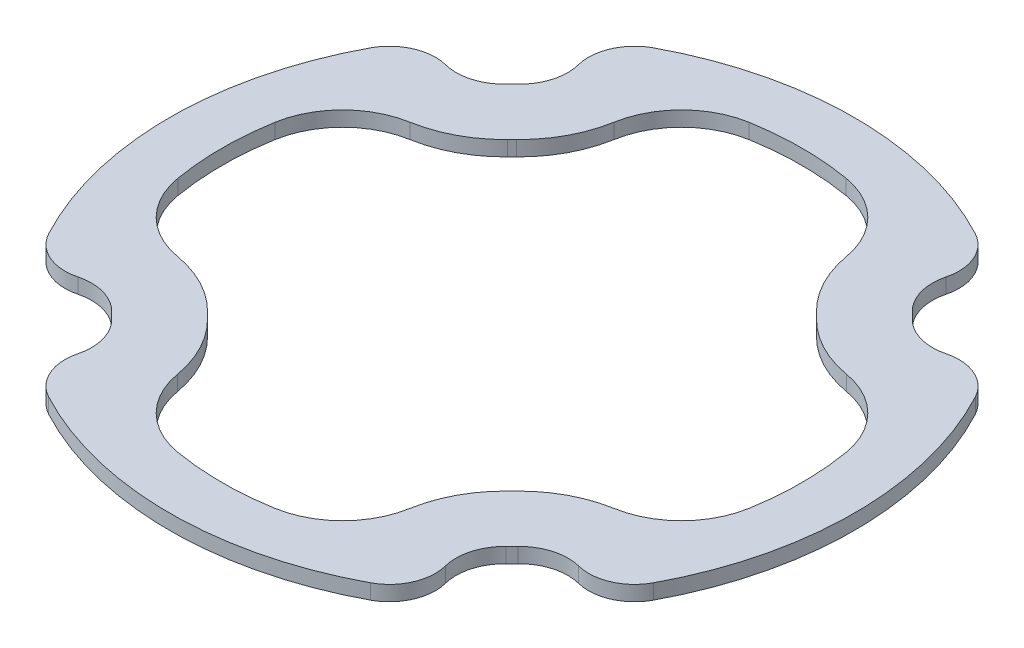
SolidWorks part; units mm, degrees
material "ABS PC"
ref_plane "Front Plane" through (0, 0, 0) normal (0, 0, 1) x (1, 0, 0)
ref_plane "Top Plane" through (0, 0, 0) normal (0, 1, 0) x (1, 0, 0)
ref_plane "Right Plane" through (0, 0, 0) normal (1, 0, 0) x (0, 0, -1)
sketch "Flange Ref" plane through (0, 0, 0) normal (0, 1, 0) x (1, 0, 0)
  arc A0 (0, 23) -> (-10.8015, 20.3058) centre (0, 0) ccw construction
  arc A1 (-10.8015, 20.3058) -> (-12.4493, 16.5701) centre (-9.2508, 17.3906) ccw construction
  arc A2 (-13.266, 13.6717) -> (-12.4493, 16.5701) centre (-15.3552, 15.8247) ccw construction
  arc A3 (-13.266, 13.6717) -> (-13.6717, 13.266) centre (0, 0) ccw construction
  arc A4 (-16.5701, 12.4493) -> (-13.6717, 13.266) centre (-15.8247, 15.3552) ccw construction
  arc A5 (-16.5701, 12.4493) -> (-17.3906, 12.5528) centre (-17.3906, 9.2508) ccw construction
  arc A6 (-17.3906, 12.5528) -> (-20.3058, 10.8015) centre (-17.3906, 9.2508) ccw construction
  arc A7 (-20.3058, 10.8015) -> (-20.3058, -10.8015) centre (0, 0) ccw construction
  circle A8 centre (0, 0) radius 25 construction
  arc A9 (10.8015, 20.3058) -> (-10.8015, 20.3058) centre (0, 0) ccw construction
  arc A10 (12.5528, 17.3906) -> (10.8015, 20.3058) centre (9.2508, 17.3906) ccw construction
  arc A11 (12.4493, 16.5701) -> (12.5528, 17.3906) centre (9.2508, 17.3906) ccw construction
  arc A12 (12.4493, 16.5701) -> (13.266, 13.6717) centre (15.3552, 15.8247) ccw construction
  arc A13 (13.6717, 13.266) -> (13.266, 13.6717) centre (0, 0) ccw construction
  arc A14 (13.6717, 13.266) -> (16.5701, 12.4493) centre (15.8247, 15.3552) ccw construction
  arc A15 (20.3058, 10.8015) -> (16.5701, 12.4493) centre (17.3906, 9.2508) ccw construction
  arc A16 (23, 0) -> (20.3058, 10.8015) centre (0, 0) ccw construction
  arc A17 (20.3058, -10.8015) -> (20.3058, 10.8015) centre (0, 0) ccw construction
  arc A18 (17.3906, -12.5528) -> (20.3058, -10.8015) centre (17.3906, -9.2508) ccw construction
  arc A19 (16.5701, -12.4493) -> (17.3906, -12.5528) centre (17.3906, -9.2508) ccw construction
  arc A20 (16.5701, -12.4493) -> (13.6717, -13.266) centre (15.8247, -15.3552) ccw construction
  arc A21 (13.266, -13.6717) -> (13.6717, -13.266) centre (0, 0) ccw construction
  arc A22 (13.266, -13.6717) -> (12.4493, -16.5701) centre (15.3552, -15.8247) ccw construction
  arc A23 (10.8015, -20.3058) -> (12.4493, -16.5701) centre (9.2508, -17.3906) ccw construction
  arc A24 (0, -23) -> (10.8015, -20.3058) centre (0, 0) ccw construction
  arc A25 (-10.8015, -20.3058) -> (10.8015, -20.3058) centre (0, 0) ccw construction
  arc A26 (-12.5528, -17.3906) -> (-10.8015, -20.3058) centre (-9.2508, -17.3906) ccw construction
  arc A27 (-12.4493, -16.5701) -> (-12.5528, -17.3906) centre (-9.2508, -17.3906) ccw construction
  arc A28 (-12.4493, -16.5701) -> (-13.266, -13.6717) centre (-15.3552, -15.8247) ccw construction
  arc A29 (-13.6717, -13.266) -> (-13.266, -13.6717) centre (0, 0) ccw construction
  arc A30 (-13.6717, -13.266) -> (-16.5701, -12.4493) centre (-15.8247, -15.3552) ccw construction
  arc A31 (-20.3058, -10.8015) -> (-16.5701, -12.4493) centre (-17.3906, -9.2508) ccw construction
  arc A32 (-23, 0) -> (-20.3058, -10.8015) centre (0, 0) ccw construction
  arc A33 (-4.75, -14.1421) -> (4.75, -14.1421) centre (0, -14.1421) ccw construction
  arc A34 (4.75, -14.1421) -> (-4.75, -14.1421) centre (0, -14.1421) ccw construction
  arc A35 (9.3921, 0) -> (18.8921, 0) centre (14.1421, 0) ccw construction
  arc A36 (18.8921, 0) -> (9.3921, 0) centre (14.1421, 0) ccw construction
  arc A37 (-4.75, 14.1421) -> (4.75, 14.1421) centre (0, 14.1421) ccw construction
  arc A38 (4.75, 14.1421) -> (-4.75, 14.1421) centre (0, 14.1421) ccw construction
  arc A39 (-18.8921, 0) -> (-9.3921, 0) centre (-14.1421, 0) ccw construction
  arc A40 (-9.3921, 0) -> (-18.8921, 0) centre (-14.1421, 0) ccw construction
  point P63 (0, 0)
  dimension "D1" = 50
sketch "Internal Slab" plane through (0, 0, 0) normal (0, 1, 0) x (1, 0, 0)
  arc A0 (20.0851, 10.6841) -> (16.6323, 12.2071) centre (17.3906, 9.2508) ccw
  arc A1 (13.4923, 13.0919) -> (16.6323, 12.2071) centre (15.8247, 15.3552) ccw
  arc A2 (12.2071, 16.6323) -> (13.0919, 13.4923) centre (15.3552, 15.8247) ccw
  arc A3 (12.3028, 17.3906) -> (10.6841, 20.0851) centre (9.2508, 17.3906) ccw
  arc A4 (12.2071, 16.6323) -> (12.3028, 17.3906) centre (9.2508, 17.3906) ccw
  arc A5 (13.4923, 13.0919) -> (13.0919, 13.4923) centre (0, 0) ccw
  arc A6 (10.6841, -20.0851) -> (12.2071, -16.6323) centre (9.2508, -17.3906) ccw
  arc A7 (13.0919, -13.4923) -> (12.2071, -16.6323) centre (15.3552, -15.8247) ccw
  arc A8 (16.6323, -12.2071) -> (13.4923, -13.0919) centre (15.8247, -15.3552) ccw
  arc A9 (17.3906, -12.3028) -> (20.0851, -10.6841) centre (17.3906, -9.2508) ccw
  arc A10 (16.6323, -12.2071) -> (17.3906, -12.3028) centre (17.3906, -9.2508) ccw
  arc A11 (13.0919, -13.4923) -> (13.4923, -13.0919) centre (0, 0) ccw
  arc A12 (-20.0851, -10.6841) -> (-16.6323, -12.2071) centre (-17.3906, -9.2508) ccw
  arc A13 (-13.4923, -13.0919) -> (-16.6323, -12.2071) centre (-15.8247, -15.3552) ccw
  arc A14 (-12.2071, -16.6323) -> (-13.0919, -13.4923) centre (-15.3552, -15.8247) ccw
  arc A15 (-12.3028, -17.3906) -> (-10.6841, -20.0851) centre (-9.2508, -17.3906) ccw
  arc A16 (-12.2071, -16.6323) -> (-12.3028, -17.3906) centre (-9.2508, -17.3906) ccw
  arc A17 (-13.4923, -13.0919) -> (-13.0919, -13.4923) centre (0, 0) ccw
  arc A18 (-20.0851, 10.6841) -> (-20.0851, -10.6841) centre (0, 0) ccw
  arc A19 (10.6841, 20.0851) -> (-10.6841, 20.0851) centre (0, 0) ccw
  arc A20 (20.0851, -10.6841) -> (20.0851, 10.6841) centre (0, 0) ccw
  arc A21 (-10.6841, -20.0851) -> (10.6841, -20.0851) centre (0, 0) ccw
  arc A122 (-10.6841, 20.0851) -> (-12.2071, 16.6323) centre (-9.2508, 17.3906) ccw
  arc A123 (-13.0919, 13.4923) -> (-13.4923, 13.0919) centre (0, 0) ccw
  arc A124 (-13.0919, 13.4923) -> (-12.2071, 16.6323) centre (-15.3552, 15.8247) ccw
  arc A125 (-16.6323, 12.2071) -> (-17.3906, 12.3028) centre (-17.3906, 9.2508) ccw
  arc A126 (-16.6323, 12.2071) -> (-13.4923, 13.0919) centre (-15.8247, 15.3552) ccw
  arc A127 (-17.3906, 12.3028) -> (-20.0851, 10.6841) centre (-17.3906, 9.2508) ccw
  arc A128 (-10.6841, 20.0851) -> (-12.2071, 16.6323) centre (-9.2508, 17.3906) ccw
  arc A129 (-13.0919, 13.4923) -> (-13.4923, 13.0919) centre (0, 0) ccw
  arc A130 (-13.0919, 13.4923) -> (-12.2071, 16.6323) centre (-15.3552, 15.8247) ccw
  arc A131 (-16.6323, 12.2071) -> (-17.3906, 12.3028) centre (-17.3906, 9.2508) ccw
  arc A132 (-16.6323, 12.2071) -> (-13.4923, 13.0919) centre (-15.8247, 15.3552) ccw
  arc A133 (-17.3906, 12.3028) -> (-20.0851, 10.6841) centre (-17.3906, 9.2508) ccw
  point P1 (0, 0)
  point P40 (0, 0)
  dimension "D1" = 0.25
  dimension "D2" = 4
extrude "PCB Outline Outer" add sketch "Internal Slab" along normal blind 1
sketch "PCB Outline Inner" plane through (0, 0, 0) normal (0, 1, 0) x (1, 0, 0)
  line L0 (0, 0) -> (-31.5542, 0) construction
  line L1 (-31.5542, 0) -> (-33.9533, 6.1655) construction
  line L2 (-33.9533, 6.1655) -> (-33.8659, 6.1654) construction
  line L3 (0, 0) -> (0, 27.5562) construction
  arc A63 (-14.5834, 8.2122) -> (-19.4715, 3.3048) centre (-13.5561, 2.3008) ccw
  arc A65 (-8.2122, 14.5834) -> (-3.3048, 19.4715) centre (-2.3008, 13.5561) cw
  arc A66 (-10.3064, 10.6216) -> (-10.6216, 10.3064) centre (0, 0) ccw
  arc A67 (-10.3064, 10.6216) -> (-8.3325, 17.6262) centre (-15.3552, 15.8247) ccw
  arc A68 (-17.6262, 8.3325) -> (-10.6216, 10.3064) centre (-15.8247, 15.3552) ccw
  arc A69 (-10.3064, 10.6216) -> (-10.6216, 10.3064) centre (0, 0) ccw
  arc A70 (-10.3064, 10.6216) -> (-8.2122, 14.5834) centre (-15.3552, 15.8247) ccw
  arc A71 (-14.5834, 8.2122) -> (-10.6216, 10.3064) centre (-15.8247, 15.3552) ccw
  arc A72 (9.2752, 17.4365) -> (-9.2752, 17.4365) centre (0, 0) ccw
  arc A73 (0, 19.75) -> (-3.3048, 19.4715) centre (0, 0) ccw
  arc A74 (3.3048, 19.4715) -> (0, 19.75) centre (0, 0) ccw
  arc A75 (8.2122, 14.5834) -> (3.3048, 19.4715) centre (2.3008, 13.5561) ccw
  arc A76 (8.2122, 14.5834) -> (10.3064, 10.6216) centre (15.3552, 15.8247) ccw
  arc A77 (10.6216, 10.3064) -> (10.3064, 10.6216) centre (0, 0) ccw
  arc A78 (10.6216, 10.3064) -> (14.5834, 8.2122) centre (15.8247, 15.3552) ccw
  arc A79 (14.5834, 8.2122) -> (19.4715, 3.3048) centre (13.5561, 2.3008) cw
  arc A80 (19.75, 0) -> (19.4715, 3.3048) centre (0, 0) ccw
  arc A81 (19.4715, -3.3048) -> (19.75, 0) centre (0, 0) ccw
  arc A82 (14.5834, -8.2122) -> (19.4715, -3.3048) centre (13.5561, -2.3008) ccw
  arc A83 (14.5834, -8.2122) -> (10.6216, -10.3064) centre (15.8247, -15.3552) ccw
  arc A84 (10.3064, -10.6216) -> (10.6216, -10.3064) centre (0, 0) ccw
  arc A85 (10.3064, -10.6216) -> (8.2122, -14.5834) centre (15.3552, -15.8247) ccw
  arc A86 (8.2122, -14.5834) -> (3.3048, -19.4715) centre (2.3008, -13.5561) cw
  arc A87 (0, -19.75) -> (3.3048, -19.4715) centre (0, 0) ccw
  arc A88 (-3.3048, -19.4715) -> (0, -19.75) centre (0, 0) ccw
  arc A89 (-8.2122, -14.5834) -> (-3.3048, -19.4715) centre (-2.3008, -13.5561) ccw
  arc A90 (-8.2122, -14.5834) -> (-10.3064, -10.6216) centre (-15.3552, -15.8247) ccw
  arc A91 (-10.6216, -10.3064) -> (-10.3064, -10.6216) centre (0, 0) ccw
  arc A92 (-10.6216, -10.3064) -> (-14.5834, -8.2122) centre (-15.8247, -15.3552) ccw
  arc A93 (-14.5834, -8.2122) -> (-19.4715, -3.3048) centre (-13.5561, -2.3008) cw
  arc A94 (-19.75, 0) -> (-19.4715, -3.3048) centre (0, 0) ccw
  arc A146 (-17.4365, 9.2752) -> (-17.4365, -9.2752) centre (0, 0) ccw
  arc A147 (-19.4715, 3.3048) -> (-19.75, 0) centre (0, 0) ccw
  point P57 (0, 0)
  dimension "D3" = 6
  dimension "D5" = 6
  dimension "D1" = 3
  dimension "D2" = 4
  dimension "D4" = 3
  dimension "D6" = 4
sketch "LED Alignment Reference" [suppressed] plane through (0, 1.6, 0) normal (0, 1, 0) x (1, 0, 0)
  line L0 (0, 0) -> (0, 23.3583)
  line L1 (0, 0) -> (6.0456, 22.5624)
  line L2 (0, 0) -> (11.6791, 20.2289)
  line L3 (0, 0) -> (16.5168, 16.5168)
  line L4 (0, 0) -> (20.2289, 11.6791)
  line L5 (0, 0) -> (22.5624, 6.0456)
  line L6 (0, 0) -> (23.3583, 0)
  line L7 (0, 0) -> (22.5624, -6.0456)
  line L8 (0, 0) -> (20.2289, -11.6791)
  line L9 (0, 0) -> (16.5168, -16.5168)
  line L10 (0, 0) -> (11.6791, -20.2289)
  line L11 (0, 0) -> (6.0456, -22.5624)
  line L12 (0, 0) -> (0, -23.3583)
  line L13 (0, 0) -> (-6.0456, -22.5624)
  line L14 (0, 0) -> (-11.6791, -20.2289)
  line L15 (0, 0) -> (-16.5168, -16.5168)
  line L16 (0, 0) -> (-20.2289, -11.6791)
  line L17 (0, 0) -> (-22.5624, -6.0456)
  line L18 (0, 0) -> (-23.3583, 0)
  line L19 (0, 0) -> (-22.5624, 6.0456)
  line L20 (0, 0) -> (-20.2289, 11.6791)
  line L21 (0, 0) -> (-16.5168, 16.5168)
  line L22 (0, 0) -> (-11.6791, 20.2289)
  line L23 (0, 0) -> (-6.0456, 22.5624)
  arc A93 (18.5401, -9.8623) -> (18.5401, 9.8623) centre (0, 0) ccw
  arc A94 (18.5401, 9.8623) -> (17.0671, 10.512) centre (17.3906, 9.2508) ccw
  arc A95 (12.2363, 11.8733) -> (17.0671, 10.512) centre (15.8247, 15.3552) ccw
  arc A96 (12.2363, 11.8733) -> (11.8733, 12.2363) centre (0, 0) ccw
  arc A97 (10.512, 17.0671) -> (11.8733, 12.2363) centre (15.3552, 15.8247) ccw
  arc A98 (10.512, 17.0671) -> (9.8623, 18.5401) centre (9.2508, 17.3906) ccw
  arc A99 (9.8623, 18.5401) -> (-9.8623, 18.5401) centre (0, 0) ccw
  arc A100 (-9.8623, 18.5401) -> (-10.512, 17.0671) centre (-9.2508, 17.3906) ccw
  arc A101 (-11.8733, 12.2363) -> (-10.512, 17.0671) centre (-15.3552, 15.8247) ccw
  arc A102 (-11.8733, 12.2363) -> (-12.2363, 11.8733) centre (0, 0) ccw
  arc A103 (-17.0671, 10.512) -> (-12.2363, 11.8733) centre (-15.8247, 15.3552) ccw
  arc A104 (-17.0671, 10.512) -> (-18.5401, 9.8623) centre (-17.3906, 9.2508) ccw
  arc A105 (-18.5401, 9.8623) -> (-18.5401, -9.8623) centre (0, 0) ccw
  arc A106 (-18.5401, -9.8623) -> (-17.0671, -10.512) centre (-17.3906, -9.2508) ccw
  arc A107 (-12.2363, -11.8733) -> (-17.0671, -10.512) centre (-15.8247, -15.3552) ccw
  arc A108 (-12.2363, -11.8733) -> (-11.8733, -12.2363) centre (0, 0) ccw
  arc A109 (-10.512, -17.0671) -> (-11.8733, -12.2363) centre (-15.3552, -15.8247) ccw
  arc A110 (-10.512, -17.0671) -> (-9.8623, -18.5401) centre (-9.2508, -17.3906) ccw
  arc A111 (-9.8623, -18.5401) -> (9.8623, -18.5401) centre (0, 0) ccw
  arc A112 (9.8623, -18.5401) -> (10.512, -17.0671) centre (9.2508, -17.3906) ccw
  arc A113 (11.8733, -12.2363) -> (10.512, -17.0671) centre (15.3552, -15.8247) ccw
  arc A114 (11.8733, -12.2363) -> (12.2363, -11.8733) centre (0, 0) ccw
  arc A115 (17.0671, -10.512) -> (12.2363, -11.8733) centre (15.8247, -15.3552) ccw
  arc A116 (17.0671, -10.512) -> (18.5401, -9.8623) centre (17.3906, -9.2508) ccw
  arc A117 (18.5401, -9.8623) -> (18.5401, 9.8623) centre (0, 0) ccw
  arc A118 (18.5401, 9.8623) -> (17.0671, 10.512) centre (17.3906, 9.2508) ccw
  arc A119 (12.2363, 11.8733) -> (17.0671, 10.512) centre (15.8247, 15.3552) ccw
  arc A120 (12.2363, 11.8733) -> (11.8733, 12.2363) centre (0, 0) ccw
  arc A121 (10.512, 17.0671) -> (11.8733, 12.2363) centre (15.3552, 15.8247) ccw
  arc A122 (10.512, 17.0671) -> (9.8623, 18.5401) centre (9.2508, 17.3906) ccw
  arc A123 (9.8623, 18.5401) -> (-9.8623, 18.5401) centre (0, 0) ccw
  arc A124 (-9.8623, 18.5401) -> (-10.512, 17.0671) centre (-9.2508, 17.3906) ccw
  arc A125 (-11.8733, 12.2363) -> (-10.512, 17.0671) centre (-15.3552, 15.8247) ccw
  arc A126 (-11.8733, 12.2363) -> (-12.2363, 11.8733) centre (0, 0) ccw
  arc A127 (-17.0671, 10.512) -> (-12.2363, 11.8733) centre (-15.8247, 15.3552) ccw
  arc A128 (-17.0671, 10.512) -> (-18.5401, 9.8623) centre (-17.3906, 9.2508) ccw
  arc A129 (-18.5401, 9.8623) -> (-18.5401, -9.8623) centre (0, 0) ccw
  arc A130 (-18.5401, -9.8623) -> (-17.0671, -10.512) centre (-17.3906, -9.2508) ccw
  arc A131 (-12.2363, -11.8733) -> (-17.0671, -10.512) centre (-15.8247, -15.3552) ccw
  arc A132 (-12.2363, -11.8733) -> (-11.8733, -12.2363) centre (0, 0) ccw
  arc A133 (-10.512, -17.0671) -> (-11.8733, -12.2363) centre (-15.3552, -15.8247) ccw
  arc A134 (-10.512, -17.0671) -> (-9.8623, -18.5401) centre (-9.2508, -17.3906) ccw
  arc A135 (-9.8623, -18.5401) -> (9.8623, -18.5401) centre (0, 0) ccw
  arc A136 (9.8623, -18.5401) -> (10.512, -17.0671) centre (9.2508, -17.3906) ccw
  arc A137 (11.8733, -12.2363) -> (10.512, -17.0671) centre (15.3552, -15.8247) ccw
  arc A138 (11.8733, -12.2363) -> (12.2363, -11.8733) centre (0, 0) ccw
  arc A139 (17.0671, -10.512) -> (12.2363, -11.8733) centre (15.8247, -15.3552) ccw
  arc A140 (17.0671, -10.512) -> (18.5401, -9.8623) centre (17.3906, -9.2508) ccw
  point P0 (0, 0)
  point P29 (0, 0)
  dimension "D2" = 1.5
  dimension "D1" = 24
sketch "Sketch7" plane through (0, 1, 0) normal (0, 1, 0) x (1, 0, 0)
  arc A56 (0, 19.25) -> (-3.2211, 18.9786) centre (0, 0) ccw
  arc A57 (-3.2211, 18.9786) -> (-7.7196, 14.4978) centre (-2.3008, 13.5561) ccw
  arc A58 (-9.9582, 10.2627) -> (-7.7196, 14.4978) centre (-15.3552, 15.8247) ccw
  arc A59 (-9.9582, 10.2627) -> (-10.2627, 9.9582) centre (0, 0) ccw
  arc A60 (-14.4978, 7.7196) -> (-10.2627, 9.9582) centre (-15.8247, 15.3552) ccw
  arc A61 (-14.4978, 7.7196) -> (-18.9786, 3.2211) centre (-13.5561, 2.3008) ccw
  arc A62 (-18.9786, 3.2211) -> (-19.25, 0) centre (0, 0) ccw
  arc A63 (-19.25, 0) -> (-18.9786, -3.2211) centre (0, 0) ccw
  arc A64 (-18.9786, -3.2211) -> (-14.4978, -7.7196) centre (-13.5561, -2.3008) ccw
  arc A65 (-10.2627, -9.9582) -> (-14.4978, -7.7196) centre (-15.8247, -15.3552) ccw
  arc A66 (-10.2627, -9.9582) -> (-9.9582, -10.2627) centre (0, 0) ccw
  arc A67 (-7.7196, -14.4978) -> (-9.9582, -10.2627) centre (-15.3552, -15.8247) ccw
  arc A68 (-7.7196, -14.4978) -> (-3.2211, -18.9786) centre (-2.3008, -13.5561) ccw
  arc A69 (-3.2211, -18.9786) -> (0, -19.25) centre (0, 0) ccw
  arc A70 (0, -19.25) -> (3.2211, -18.9786) centre (0, 0) ccw
  arc A71 (3.2211, -18.9786) -> (7.7196, -14.4978) centre (2.3008, -13.5561) ccw
  arc A72 (9.9582, -10.2627) -> (7.7196, -14.4978) centre (15.3552, -15.8247) ccw
  arc A73 (9.9582, -10.2627) -> (10.2627, -9.9582) centre (0, 0) ccw
  arc A74 (14.4978, -7.7196) -> (10.2627, -9.9582) centre (15.8247, -15.3552) ccw
  arc A75 (14.4978, -7.7196) -> (18.9786, -3.2211) centre (13.5561, -2.3008) ccw
  arc A76 (18.9786, -3.2211) -> (19.25, 0) centre (0, 0) ccw
  arc A77 (19.25, 0) -> (18.9786, 3.2211) centre (0, 0) ccw
  arc A78 (18.9786, 3.2211) -> (14.4978, 7.7196) centre (13.5561, 2.3008) ccw
  arc A79 (10.2627, 9.9582) -> (14.4978, 7.7196) centre (15.8247, 15.3552) ccw
  arc A80 (10.2627, 9.9582) -> (9.9582, 10.2627) centre (0, 0) ccw
  arc A81 (7.7196, 14.4978) -> (9.9582, 10.2627) centre (15.3552, 15.8247) ccw
  arc A82 (7.7196, 14.4978) -> (3.2211, 18.9786) centre (2.3008, 13.5561) ccw
  arc A83 (3.2211, 18.9786) -> (0, 19.25) centre (0, 0) ccw
  arc A84 (0, 19.25) -> (-3.2211, 18.9786) centre (0, 0) ccw
  arc A85 (-3.2211, 18.9786) -> (-7.7196, 14.4978) centre (-2.3008, 13.5561) ccw
  arc A86 (-9.9582, 10.2627) -> (-7.7196, 14.4978) centre (-15.3552, 15.8247) ccw
  arc A87 (-9.9582, 10.2627) -> (-10.2627, 9.9582) centre (0, 0) ccw
  arc A88 (-14.4978, 7.7196) -> (-10.2627, 9.9582) centre (-15.8247, 15.3552) ccw
  arc A89 (-14.4978, 7.7196) -> (-18.9786, 3.2211) centre (-13.5561, 2.3008) ccw
  arc A90 (-18.9786, 3.2211) -> (-19.25, 0) centre (0, 0) ccw
  arc A91 (-19.25, 0) -> (-18.9786, -3.2211) centre (0, 0) ccw
  arc A92 (-18.9786, -3.2211) -> (-14.4978, -7.7196) centre (-13.5561, -2.3008) ccw
  arc A93 (-10.2627, -9.9582) -> (-14.4978, -7.7196) centre (-15.8247, -15.3552) ccw
  arc A94 (-10.2627, -9.9582) -> (-9.9582, -10.2627) centre (0, 0) ccw
  arc A95 (-7.7196, -14.4978) -> (-9.9582, -10.2627) centre (-15.3552, -15.8247) ccw
  arc A96 (-7.7196, -14.4978) -> (-3.2211, -18.9786) centre (-2.3008, -13.5561) ccw
  arc A97 (-3.2211, -18.9786) -> (0, -19.25) centre (0, 0) ccw
  arc A98 (0, -19.25) -> (3.2211, -18.9786) centre (0, 0) ccw
  arc A99 (3.2211, -18.9786) -> (7.7196, -14.4978) centre (2.3008, -13.5561) ccw
  arc A100 (9.9582, -10.2627) -> (7.7196, -14.4978) centre (15.3552, -15.8247) ccw
  arc A101 (9.9582, -10.2627) -> (10.2627, -9.9582) centre (0, 0) ccw
  arc A102 (14.4978, -7.7196) -> (10.2627, -9.9582) centre (15.8247, -15.3552) ccw
  arc A103 (14.4978, -7.7196) -> (18.9786, -3.2211) centre (13.5561, -2.3008) ccw
  arc A104 (18.9786, -3.2211) -> (19.25, 0) centre (0, 0) ccw
  arc A105 (19.25, 0) -> (18.9786, 3.2211) centre (0, 0) ccw
  arc A106 (18.9786, 3.2211) -> (14.4978, 7.7196) centre (13.5561, 2.3008) ccw
  arc A107 (10.2627, 9.9582) -> (14.4978, 7.7196) centre (15.8247, 15.3552) ccw
  arc A108 (10.2627, 9.9582) -> (9.9582, 10.2627) centre (0, 0) ccw
  arc A109 (7.7196, 14.4978) -> (9.9582, 10.2627) centre (15.3552, 15.8247) ccw
  arc A110 (7.7196, 14.4978) -> (3.2211, 18.9786) centre (2.3008, 13.5561) ccw
  arc A111 (3.2211, 18.9786) -> (0, 19.25) centre (0, 0) ccw
  point P62 (-2.8434, -19.3)
  dimension "D1" = 0.5
extrude "Cut-Extrude2" cut sketch "Sketch7" against normal through all both and the other way through all
